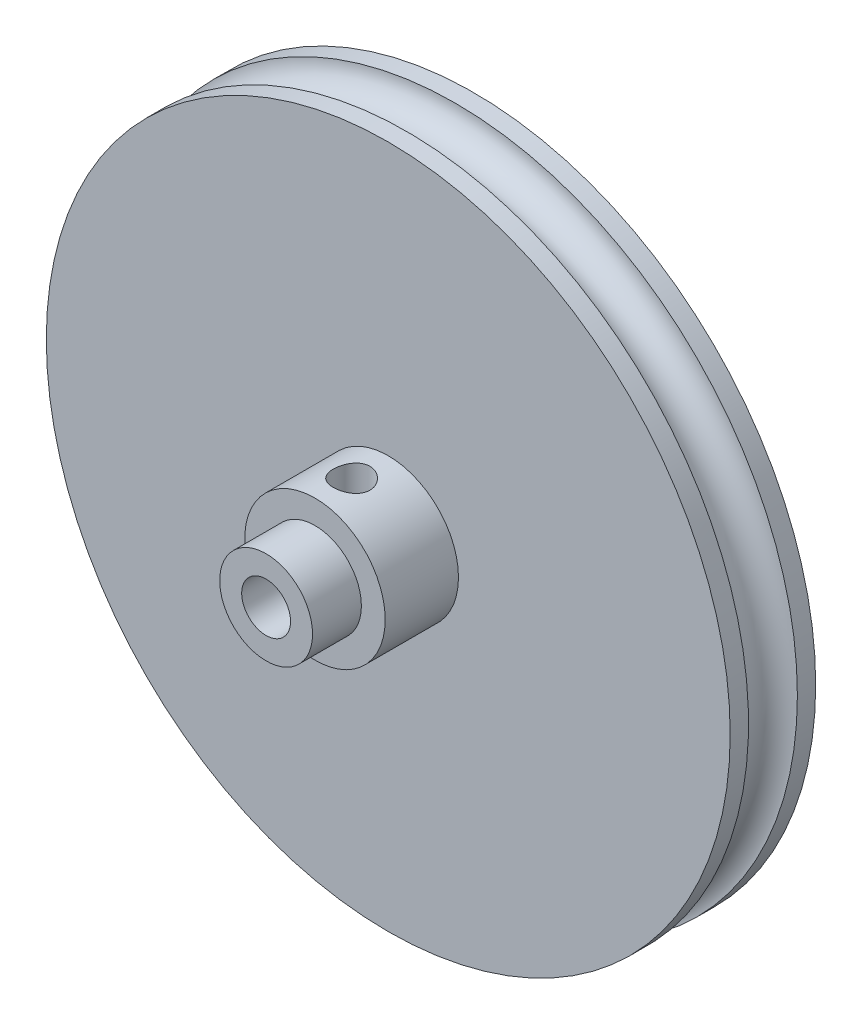
SolidWorks part; units mm, degrees
ref_plane "Plan de face" through (0, 0, 0) normal (0, 0, 1) x (1, 0, 0)
ref_plane "Plan de dessus" through (0, 0, 0) normal (0, 1, 0) x (1, 0, 0)
ref_plane "Plan de droite" through (0, 0, 0) normal (1, 0, 0) x (0, 0, -1)
sketch "Esquisse1" plane through (0, 0, 0) normal (0, 0, 1) x (1, 0, 0)
  circle A0 centre (0, 0) radius 28
  dimension "D1" = 56
extrude "Boss.-Extru.1" add sketch "Esquisse1" along normal blind 7
sketch "Esquisse2" plane through (0, 0, 7) normal (0, 0, 1) x (1, 0, 0)
  circle A0 centre (0, 0) radius 3.8
  dimension "D1" = 7.6
extrude "Boss.-Extru.2" add sketch "Esquisse2" along normal blind 10
sketch "Esquisse3" plane through (0, 0, 17) normal (0, 0, 1) x (1, 0, 0)
  circle A0 centre (0, 0) radius 2
  dimension "D1" = 4
extrude "Enlèv. mat.-Extru.1" cut sketch "Esquisse3" against normal through all
sketch "Esquisse4" plane through (0, 0, 0) normal (1, 0, 0) x (0, 0, -1)
  line L0 (-3.5, 28) -> (-3.5, 8.0945) construction
  line L1 (0, 28) -> (-7, 28) construction
  line L2 (0, 0) -> (-21.8888, 0) construction
  line L3 (-3.5, 0) -> (-3.5, -28) construction
  circle A1 centre (-3.5, 28) radius 2
  circle A2 centre (-3.5, -28) radius 2 construction
  dimension "D1" = 4
revolve "Enlèvement de matière-Révolution1" cut sketch "Esquisse4" angle 360 about L2
sketch "Esquisse5" plane through (0, 0, 7) normal (0, 0, 1) x (1, 0, 0)
  circle A0 centre (0, 0) radius 3.8
  circle A1 centre (0, 0) radius 5.75
  dimension "D1" = 11.5
  dimension "D2" = 7.6
extrude "Boss.-Extru.3" add sketch "Esquisse5" along normal blind 6
sketch "Esquisse6" plane through (0, 0, 0) normal (0, 1, 0) x (1, 0, 0)
  line L0 (0, -13) -> (0, -7) construction
  line L1 (-3.8, -13) -> (3.8, -13) construction
  line L2 (-5.75, -7) -> (5.75, -7) construction
  circle A0 centre (0, -10) radius 1.5
extrude "Enlèv. mat.-Extru.2" cut sketch "Esquisse6" along normal up to next
